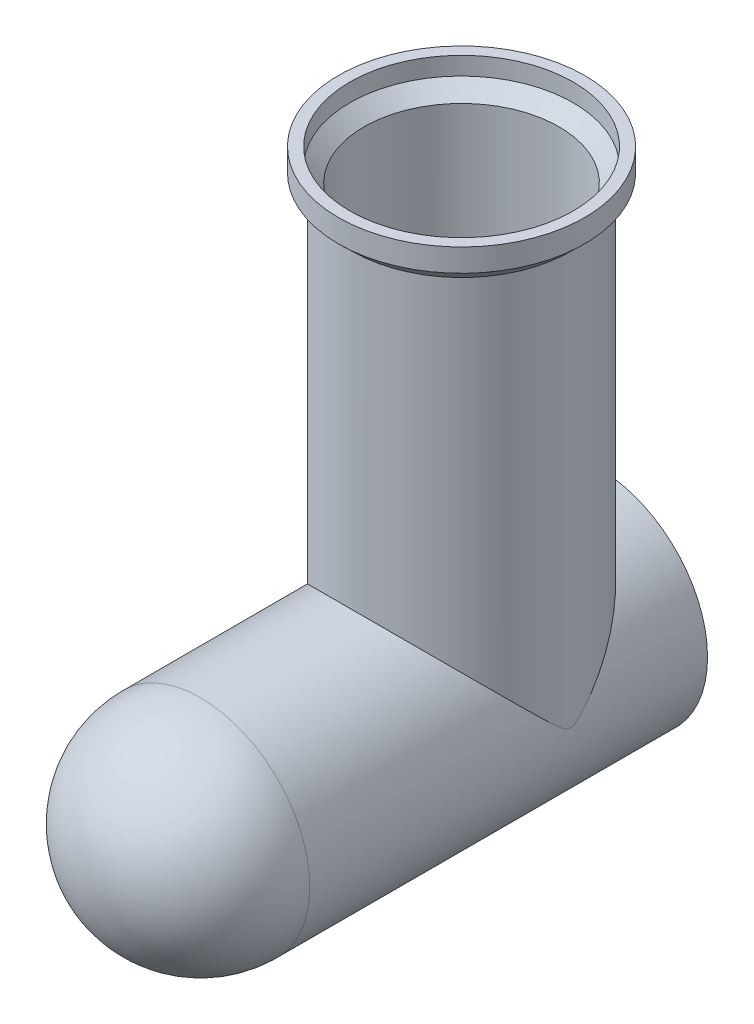
SolidWorks part; units mm, degrees
material "2014-T4"
ref_plane "Front Plane" through (0, 0, 0) normal (0, 0, 1) x (1, 0, 0)
ref_plane "Top Plane" through (0, 0, 0) normal (0, 1, 0) x (1, 0, 0)
ref_plane "Right Plane" through (0, 0, 0) normal (1, 0, 0) x (0, 0, -1)
sketch "Sketch1" plane through (0, 0, 0) normal (0, 0, 1) x (1, 0, 0)
  circle A0 centre (0, 0) radius 47.85
  dimension "D1" = 95.7
extrude "Boss-Extrude1" add sketch "Sketch1" along normal blind 222.25
ref_plane "Plane1" through (0, 183.95, 0) normal (0, 1, 0) x (1, 0, 0)
sketch "Sketch2" plane through (0, 183.95, 0) normal (0, 1, 0) x (1, 0, 0)
  circle A0 centre (0, -60) radius 47.75
  point P0 (0, 0)
  dimension "D1" = 95.5
  dimension "D2" = 60
extrude "Boss-Extrude2" add sketch "Sketch2" against normal blind 183.95
sketch "Sketch5" plane through (0, 0, 0) normal (1, 0, 0) x (0, 0, -1)
  line L0 (-12.25, 183.95) -> (-107.75, 183.95) construction
  line L1 (-12.25, 183.95) -> (-107.75, 183.95)
  line L2 (-12.25, 183.95) -> (-6.025, 189.95)
  line L3 (-6.025, 189.95) -> (-6.025, 199.95)
  line L4 (-6.025, 199.95) -> (-60, 199.95)
  line L5 (-60, 199.95) -> (-60, 183.95)
  dimension "D1" = 16
  dimension "D2" = 6
  dimension "D3" = 53.975
revolve "Revolve3" add sketch "Sketch5" angle 360 about L5
fillet "Fillet1" radius 47.85 1 edges at (47.85, 0, 222.25)
shell "Shell1" thickness 5
